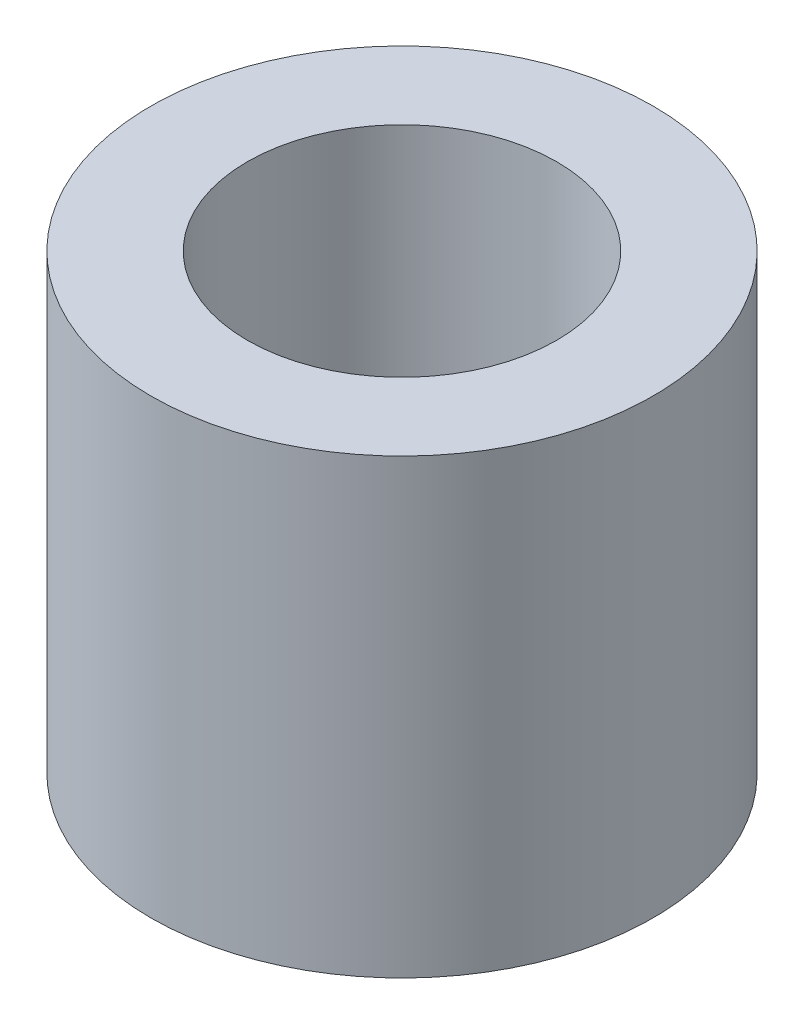
SolidWorks part; units mm, degrees
ref_plane "Front Plane" through (0, 0, 0) normal (0, 0, 1) x (1, 0, 0)
ref_plane "Top Plane" through (0, 0, 0) normal (0, 1, 0) x (1, 0, 0)
ref_plane "Right Plane" through (0, 0, 0) normal (1, 0, 0) x (0, 0, -1)
sketch "Sketch1" plane through (0, 0, 0) normal (0, 1, 0) x (1, 0, 0)
  circle A0 centre (0, 0) radius 2.4447
  circle A1 centre (0, 0) radius 3.9688
  dimension "D1" = 4.8895
  dimension "D2" = 7.9375
extrude "Boss-Extrude1" add sketch "Sketch1" along normal blind 7.1437
